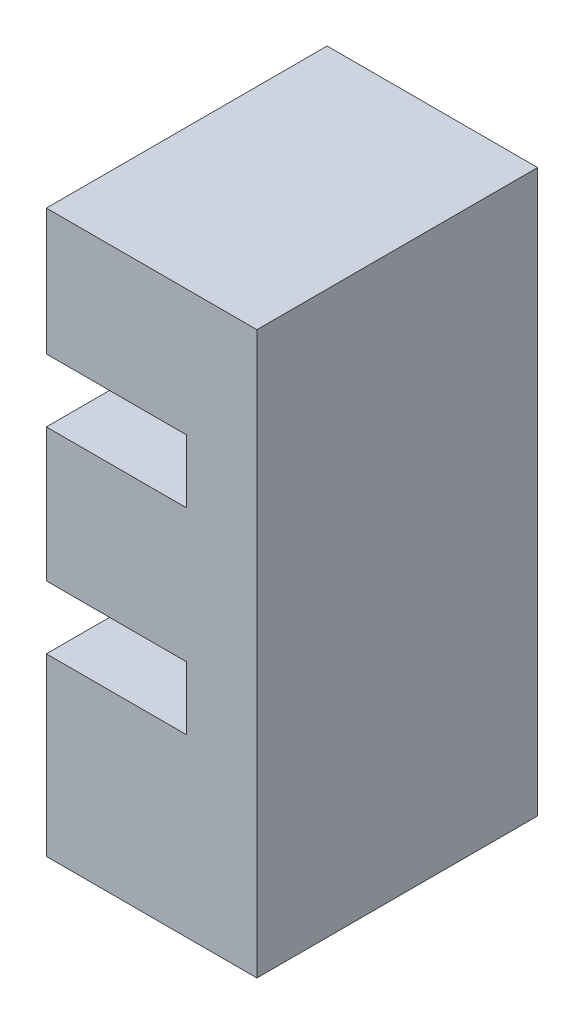
SolidWorks part; units mm, degrees
ref_plane "Front Plane" through (0, 0, 0) normal (0, 0, 1) x (1, 0, 0)
ref_plane "Top Plane" through (0, 0, 0) normal (0, 1, 0) x (1, 0, 0)
ref_plane "Right Plane" through (0, 0, 0) normal (1, 0, 0) x (0, 0, -1)
sketch "Sketch1" plane through (0, 0, 0) normal (0, 0, 1) x (1, 0, 0)
  line L0 (-1.905, 1.143) -> (-1.905, -1.27)
  line L1 (-1.905, 4.572) -> (1.905, 4.572)
  line L2 (-1.905, -2.413) -> (-1.905, -5.588)
  line L3 (-1.905, -5.588) -> (1.905, -5.588)
  line L4 (1.905, 4.572) -> (1.905, -5.588)
  line L7 (-1.905, 1.143) -> (0.635, 1.143)
  line L8 (0.635, 1.143) -> (0.635, 2.286)
  line L9 (0.635, 2.286) -> (-1.905, 2.286)
  line L11 (-1.905, -1.27) -> (0.635, -1.27)
  line L12 (0.635, -1.27) -> (0.635, -2.413)
  line L13 (0.635, -2.413) -> (-1.905, -2.413)
  line L14 (-1.905, 2.286) -> (-1.905, 4.572)
  point P0 (0, 0)
  point P9 (-1.905, -0.0635)
  dimension "D1" = 3.81
  dimension "D2" = 10.16
  dimension "D3" = 2.413
  dimension "D4" = 2.54
  dimension "D5" = 1.143
  dimension "D6" = 1.143
  dimension "D7" = 3.175
extrude "Boss-Extrude3" add sketch "Sketch1" along normal blind 5.08
